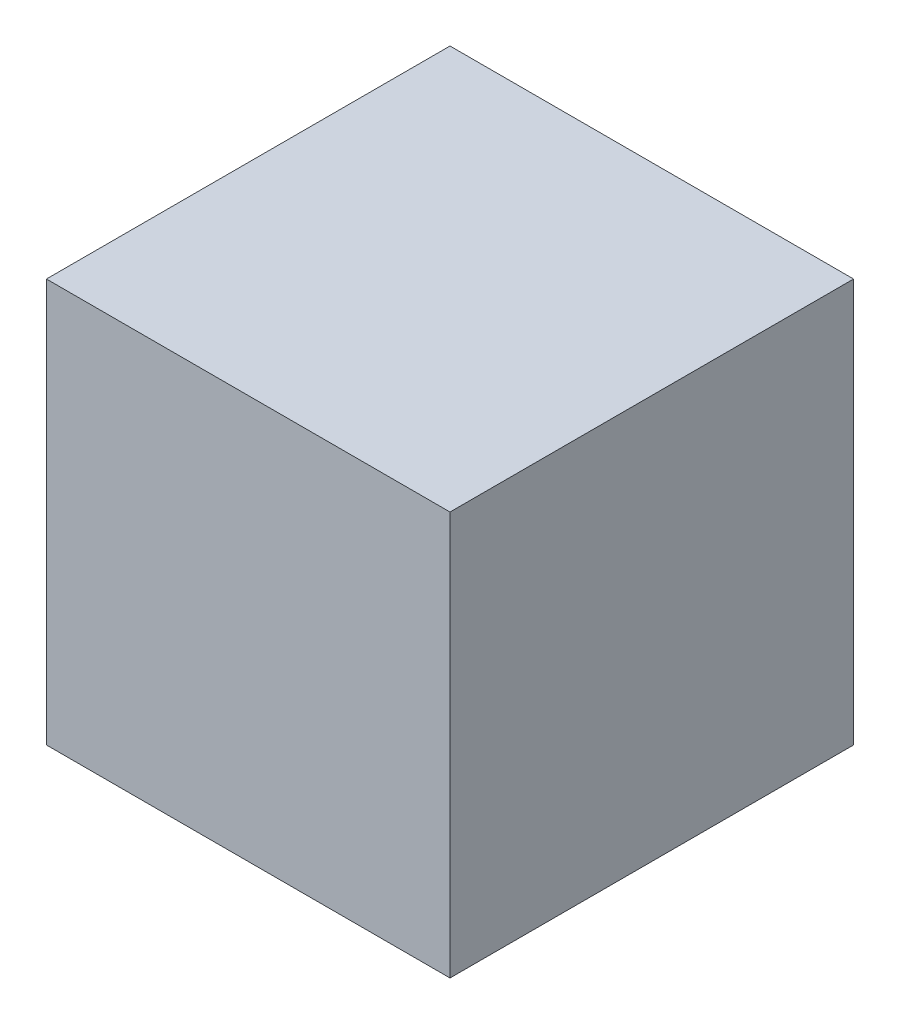
SolidWorks part; units mm, degrees
ref_plane "Front Plane" through (0, 0, 0) normal (0, 0, 1) x (1, 0, 0)
ref_plane "Top Plane" through (0, 0, 0) normal (0, 1, 0) x (1, 0, 0)
ref_plane "Right Plane" through (0, 0, 0) normal (1, 0, 0) x (0, 0, -1)
sketch "Sketch1" plane through (0, 0, 0) normal (0, 1, 0) x (1, 0, 0)
  line L1 (0, 0) -> (14, 0)
  line L2 (0, 0) -> (0, -14)
  line L3 (0, -14) -> (14, -14)
  line L4 (14, 0) -> (14, -14)
  dimension "D1" = 14
  dimension "D2" = 14
extrude "Boss-Extrude1" add sketch "Sketch1" along normal blind 14
